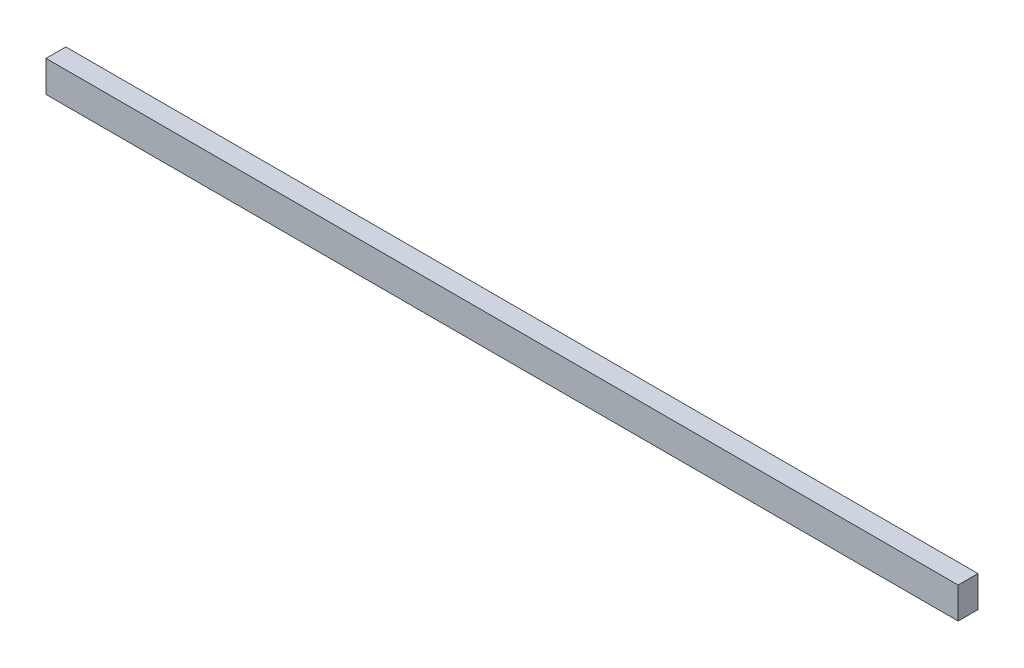
SolidWorks part; units mm, degrees
material "Pine"
ref_plane "Front Plane" through (0, 0, 0) normal (0, 0, 1) x (1, 0, 0)
ref_plane "Top Plane" through (0, 0, 0) normal (0, 1, 0) x (1, 0, 0)
ref_plane "Right Plane" through (0, 0, 0) normal (1, 0, 0) x (0, 0, -1)
sketch "Sketch1" plane through (0, 0, 0) normal (0, 0, 1) x (1, 0, 0)
  line L1 (-146.05, -5) -> (146.05, -5)
  line L2 (-146.05, -5) -> (-146.05, 5)
  line L3 (-146.05, 5) -> (146.05, 5)
  line L4 (146.05, -5) -> (146.05, 5)
  line L5 (-146.05, -5) -> (146.05, 5) construction
  line L6 (-146.05, 5) -> (146.05, -5) construction
  point P0 (0, 0)
  dimension "D1" = 10
  dimension "D2" = 292.1
extrude "Boss-Extrude1" add sketch "Sketch1" along normal blind 6.35
